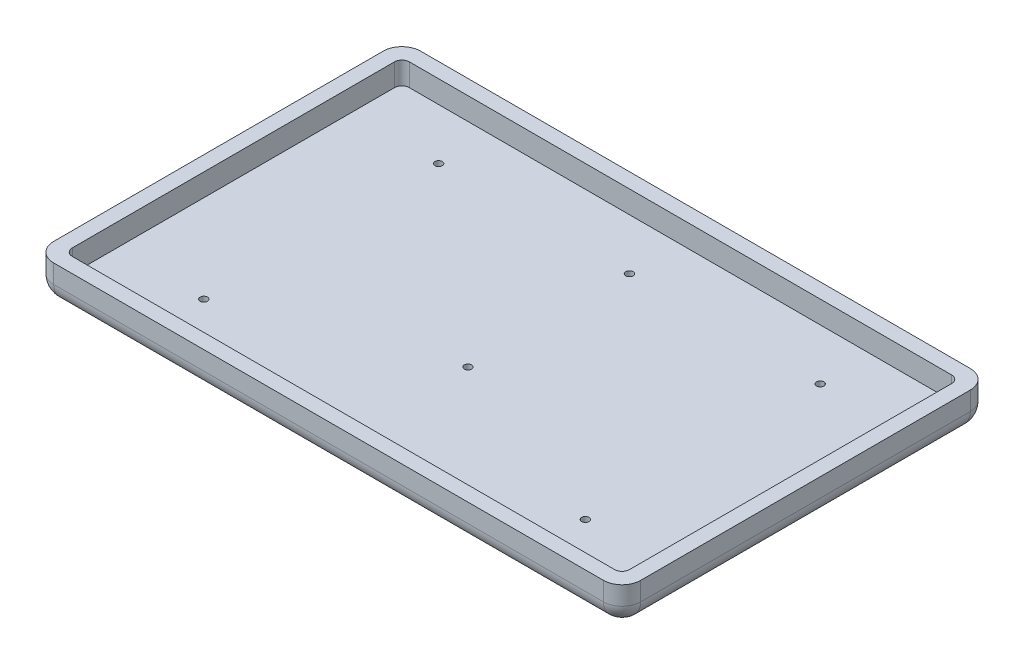
SolidWorks part; units mm, degrees
ref_plane "Front Plane" through (0, 0, 0) normal (0, 0, 1) x (1, 0, 0)
ref_plane "Top Plane" through (0, 0, 0) normal (0, 1, 0) x (1, 0, 0)
ref_plane "Right Plane" through (0, 0, 0) normal (1, 0, 0) x (0, 0, -1)
sketch "Sketch1" plane through (0, 0, 0) normal (0, 1, 0) x (1, 0, 0)
  line L1 (-100, 62.5) -> (100, 62.5)
  line L2 (-100, 62.5) -> (-100, -62.5)
  line L3 (-100, -62.5) -> (100, -62.5)
  line L4 (100, 62.5) -> (100, -62.5)
  point P4 (-100, 0)
  point P6 (0, 62.5)
  dimension "D1" = 125
  dimension "D2" = 200
extrude "Boss-Extrude1" add sketch "Sketch1" along normal blind 12.7
sketch "Sketch2" plane through (0, 12.7, 0) normal (0, 1, 0) x (1, 0, 0)
  line L0 (-100, 62.5) -> (-100, -62.5) construction
  line L1 (-94.92, 57.42) -> (94.92, 57.42)
  line L2 (-94.92, 57.42) -> (-94.92, -57.42)
  line L3 (-94.92, -57.42) -> (94.92, -57.42)
  line L4 (94.92, 57.42) -> (94.92, -57.42)
  line L5 (-94.92, 57.42) -> (94.92, -57.42) construction
  line L6 (-94.92, -57.42) -> (94.92, 57.42) construction
  line L7 (-100, -62.5) -> (100, -62.5) construction
  point P0 (0, 0)
  dimension "D1" = 5.08
  dimension "D2" = 5.08
extrude "Cut-Extrude1" cut sketch "Sketch2" against normal blind 7.62
fillet "Fillet1" radius 2.54 4 edges at (-94.92, 8.89, 57.42) (94.92, 8.89, 57.42) (94.92, 8.89, -57.42) (-94.92, 8.89, -57.42)
fillet "Fillet2" radius 6.35 4 edges at (-100, 6.35, 62.5) (-100, 6.35, -62.5) (100, 6.35, -62.5) (100, 6.35, 62.5)
fillet "Fillet3" radius 6.35 8 edges at (98.1401, 0, -60.6401) (98.1401, 0, 60.6401) (-98.1401, 0, 60.6401) (-98.1401, 0, -60.6401) (-100, 0, 0) (0, 0, 62.5) (100, 0, 0) (0, 0, -62.5)
hole_wizard "M3x0.5 Tapped Hole1" positions "Sketch3" profile "Sketch4" tap size "M3x0.5" standard "ANSI Metric" end condition through all
sketch "Sketch3" plane through (0, 5.08, 0) normal (0, 1, 0) x (1, 0, 0)
  line L1 (-75, 50) -> (75, 50)
  line L2 (-75, 50) -> (-75, -50)
  line L3 (-75, -50) -> (75, -50)
  line L4 (75, 50) -> (75, -50)
  line L5 (-75, 50) -> (75, -50) construction
  line L6 (-75, -50) -> (75, 50) construction
  point P60 (-65, 40)
  point P62 (65, 40)
  point P64 (65, -40)
  point P66 (-65, -40)
  point P68 (0, 40)
  point P70 (0, -15)
  point P74 (0, 0)
  point P75 (0, 0)
  point P76 (0, 0)
  point P77 (0, 0)
  point P78 (0, 0)
  point P80 (0, 0)
  dimension "D1" = 150
  dimension "D2" = 100
  dimension "D3" = 10
  dimension "D4" = 10
  dimension "D5" = 35
  dimension "D6" = 10
  dimension "D7" = 10
sketch "Sketch4" plane through (0, 5.08, 15) normal (1, 0, 0) x (0, 0, 1)
  line L0 (0, 0) -> (0, 5.08)
  line L1 (0, 5.08) -> (1.25, 5.08)
  line L2 (1.25, 5.08) -> (1.25, 0)
  line L5 (1.25, 0) -> (0, 0)
  line L11 (0, -6.35) -> (0, 107.95) construction
  dimension "Thru Tap Drill Dia." = 2.5
  dimension "Thru Tap Drill Depth" = 5.08
cosmetic thread "Hole Thread1" parameters "D2"=3
cosmetic thread "Hole Thread2" parameters "D2"=3
cosmetic thread "Hole Thread3" parameters "D2"=3
cosmetic thread "Hole Thread4" parameters "D2"=3
cosmetic thread "Hole Thread5" parameters "D2"=3
cosmetic thread "Hole Thread6" parameters "D2"=3
